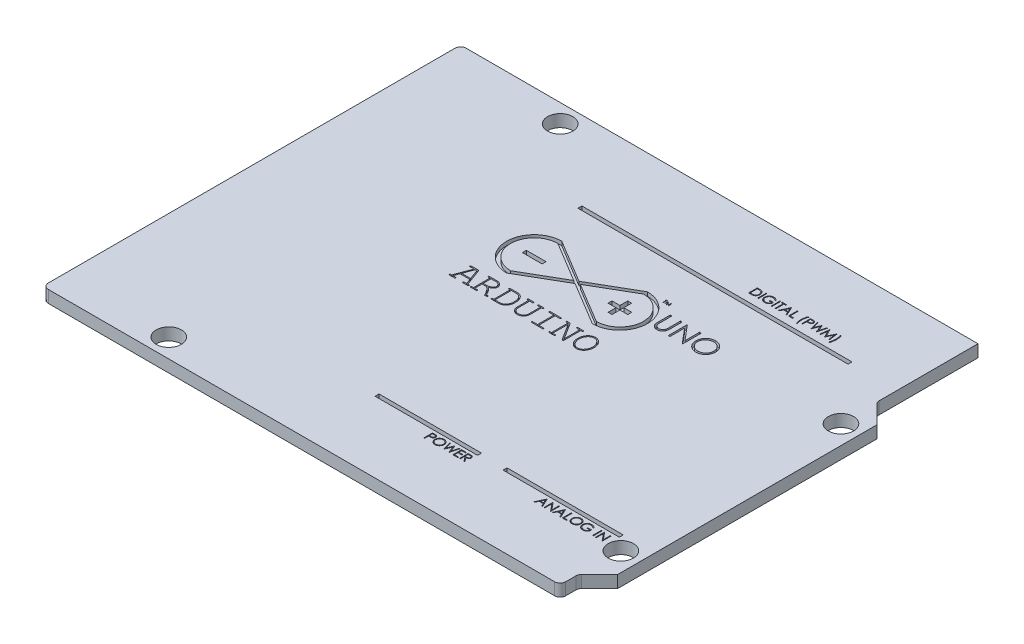
SolidWorks part; units mm, degrees
ref_plane "Plan de face" through (0, 0, 0) normal (0, 0, 1) x (1, 0, 0)
ref_plane "Plan de dessus" through (0, 0, 0) normal (0, 1, 0) x (1, 0, 0)
ref_plane "Plan de droite" through (0, 0, 0) normal (1, 0, 0) x (0, 0, -1)
sketch "Esquisse1" plane through (0, 0, 0) normal (0, 1, 0) x (1, 0, 0)
  line L0 (65.7, 53.05) -> (65.7, 40.2)
  line L1 (0, 0) -> (65.7, 0)
  line L2 (0, 0) -> (0, 53.05)
  line L3 (0, 53.05) -> (65.7, 53.05)
  line L4 (68.2, 4.8) -> (68.2, 37.7)
  line L5 (65.7, 40.2) -> (68.2, 37.7)
  line L6 (68.2, 4.8) -> (65.7, 2.3)
  line L7 (65.7, 2.3) -> (65.7, 0)
  circle A0 centre (15, 50.7) radius 1.6
  circle A1 centre (13.6, 2.4) radius 1.6
  circle A2 centre (65.8, 7.6) radius 1.6
  circle A3 centre (65.8, 35.55) radius 1.6
  dimension "D8" = 3.2
  dimension "D9" = 3.2
  dimension "D10" = 3.2
  dimension "D11" = 3.2
  dimension "D12" = 2.4
  dimension "D13" = 27.95
  dimension "D14" = 7.6
  dimension "D15" = 2.4
  dimension "D16" = 15
  dimension "D17" = 2.35
  dimension "D18" = 2.4
  dimension "D19" = 13.6
  dimension "D1" = 53.05
  dimension "D2" = 68.2
  dimension "D3" = 2.5
  dimension "D4" = 135
  dimension "D5" = 135
  dimension "D6" = 32.9
  dimension "D7" = 2.3
extrude "Boss.-Extru.1" add sketch "Esquisse1" along normal blind 1.55
fillet "Congé1" radius 0.7 5 edges at (65.7, 0.775, -40.2) (65.7, 0.775, -2.3) (65.7, 0.775, 0) (0, 0.775, -53.05) (0, 0.775, 0)
sketch "Sketch1" plane through (0, 1.55, 0) normal (0, 1, 0) x (1, 0, 0)
  line L0 (65.7, 53.05) -> (0.7, 53.05) construction
  line L1 (25.4017, 42.55) -> (59.7, 42.55)
  line L2 (25.4017, 43.05) -> (59.7, 43.05)
  line L3 (25.4017, 43.05) -> (25.4017, 42.55)
  line L4 (59.7, 43.05) -> (59.7, 42.55)
  line L5 (59.7, 42.55) -> (59.7448, 42.6405)
  line L6 (65.7, 40.4899) -> (65.7, 53.05) construction
  dimension "D1" = 0.5
  dimension "D2" = 10
  dimension "D3" = 6
extrude "Cut-Extrude1" cut sketch "Sketch1" against normal blind 0.5 contours L1 L3 L2 L4
sketch "Sketch2" plane through (0, 1.55, 0) normal (0, 1, 0) x (1, 0, 0)
  line L0 (57.7, 44.0663) -> (44.1775, 44.0663) construction
  line L1 (25.4017, 43.05) -> (59.7, 43.05) construction
  line L2 (65.7, 40.4899) -> (65.7, 53.05) construction
  text T0 "DIGITAL (PWM)" font "Century Gothic" height 1.1167
  dimension "D1" = 1.0163
  dimension "D2" = 8
extrude "Cut-Extrude2" cut sketch "Sketch2" against normal blind 0.5
sketch "Sketch3" plane through (0, 1.55, 0) normal (0, 1, 0) x (1, 0, 0)
  line L0 (0.7, 0) -> (65, 0) construction
  line L1 (33.2, 9.5) -> (46.2, 9.5)
  line L2 (33.2, 9.5) -> (33.2, 9)
  line L3 (33.2, 9) -> (46.2, 9)
  line L4 (46.2, 9.5) -> (46.2, 9)
  line L5 (49.45, 9.5) -> (64.2, 9.5)
  line L6 (49.45, 9.5) -> (49.45, 9)
  line L7 (49.45, 9) -> (64.2, 9)
  line L8 (64.2, 9.5) -> (64.2, 9)
  line L9 (63.7, 7.5) -> (53.3998, 7.5) construction
  line L10 (46.2, 7.5) -> (34.2198, 7.5) construction
  line L11 (68.2, 4.8) -> (68.2, 37.7) construction
  text T0 "POWER" font "Century Gothic" height 1.1167
  text T1 "ANALOG IN" font "Century Gothic" height 1.1167
  dimension "D1" = 9
  dimension "D2" = 9
  dimension "D3" = 0.5
  dimension "D4" = 0.5
  dimension "D5" = 13
  dimension "D6" = 14.75
  dimension "D7" = 1.5
  dimension "D8" = 22
  dimension "D9" = 22
  dimension "D10" = 4
  dimension "D11" = 4.5
extrude "Cut-Extrude3" cut sketch "Sketch3" against normal blind 0.5
sketch "Sketch5" plane through (0, 1.55, 0) normal (0, 1, 0) x (1, 0, 0)
  line L0 (28.004, 37.3981) -> (33.0823, 34.3397)
  line L1 (28.004, 30.8981) -> (33.5055, 34.0849)
  line L2 (39.007, 37.7716) -> (33.5055, 34.5849)
  line L3 (39.007, 31.2716) -> (33.9287, 34.33)
  line L4 (33.9287, 34.33) -> (39.007, 37.2716)
  line L5 (33.0823, 34.3397) -> (28.004, 31.3981)
  line L6 (33.5055, 34.5849) -> (28.004, 37.8981)
  line L7 (33.5055, 34.0849) -> (39.007, 30.7716)
  line L8 (39.257, 34.5216) -> (39.257, 35.5216)
  line L9 (26.754, 34.1481) -> (29.254, 34.1481)
  line L10 (26.754, 34.1481) -> (26.754, 34.6481)
  line L11 (26.754, 34.6481) -> (29.254, 34.6481)
  line L12 (29.254, 34.1481) -> (29.254, 34.6481)
  line L13 (26.754, 34.1481) -> (29.254, 34.6481) construction
  line L14 (26.754, 34.6481) -> (29.254, 34.1481) construction
  line L15 (37.757, 34.0216) -> (38.757, 34.0216)
  line L16 (37.757, 34.0216) -> (37.757, 34.5216)
  line L17 (37.757, 34.5216) -> (38.757, 34.5216)
  line L18 (40.257, 34.0216) -> (40.257, 34.5216)
  line L21 (38.757, 33.0216) -> (39.257, 33.0216)
  line L22 (39.257, 34.5216) -> (40.257, 34.5216)
  line L23 (38.757, 35.5216) -> (39.257, 35.5216)
  line L24 (39.257, 33.0216) -> (39.257, 34.0216)
  line L27 (38.757, 33.0216) -> (38.757, 34.0216)
  line L28 (38.757, 34.5216) -> (38.757, 35.5216)
  line L29 (39.257, 34.0216) -> (40.257, 34.0216)
  arc A2 (28.004, 37.3981) -> (28.004, 31.3981) centre (28.004, 34.3981) ccw
  arc A3 (39.007, 31.2716) -> (39.007, 37.2716) centre (39.007, 34.2716) ccw
  arc A4 (39.007, 30.7716) -> (39.007, 37.7716) centre (39.007, 34.2716) ccw
  arc A6 (28.004, 37.8981) -> (28.004, 30.8981) centre (28.004, 34.3981) ccw
  dimension "D1" = 0.5
  dimension "D2" = 2.5
  dimension "D3" = 6
  dimension "D4" = 6
  dimension "D5" = 0.5
  dimension "D6" = 0.5
  dimension "D7" = 2.5
  dimension "D8" = 2.5
extrude "Cut-Extrude4" cut sketch "Sketch5" against normal blind 0.5 contours L24 L29 L18 L22 L8 L23 L28 L17 L16 L15 L27 L21 | L6 A6 L1 L7 A4 L2 A2 L0 L5 A3 L3 L4 | L9 L12 L11 L10
sketch "Sketch6" plane through (0, 1.55, 0) normal (0, 1, 0) x (1, 0, 0)
  line L0 (24.504, 27.05) -> (42.507, 27.05) construction
  line L1 (42.7, 34.2716) -> (49.2, 34.2716) construction
  line L2 (40.5, 37.55) -> (42.5, 37.55) construction
  line L3 (65.7, 53.05) -> (0.7, 53.05) construction
  line L4 (68.2, 4.8) -> (68.2, 37.7) construction
  line L5 (0, 52.35) -> (0, 0.7) construction
  text T0 "ARDUINO" font "Courier New" height in points 11
  text T1 "UNO" font "Century Gothic" height in points 9
  text T2 "TM" font "Century Gothic" height 0.5
  dimension "D1" = 26
  dimension "D2" = 19
  dimension "D3" = 6.5
  dimension "D4" = 15.5
  dimension "D5" = 2
  dimension "D6" = 40.5
extrude "Cut-Extrude5" cut sketch "Sketch6" against normal blind 0.5
